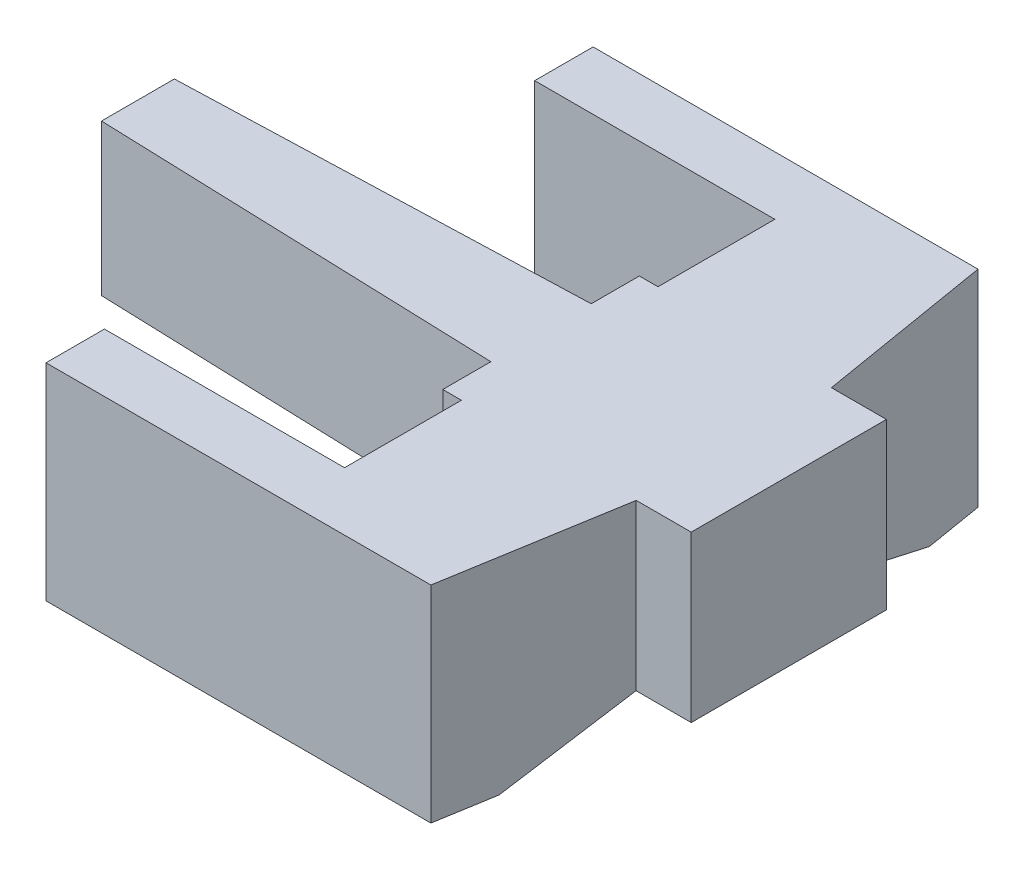
SolidWorks part; units mm, degrees
ref_plane "Front Plane" through (0, 0, 0) normal (0, 0, 1) x (1, 0, 0)
ref_plane "Top Plane" through (0, 0, 0) normal (0, 1, 0) x (1, 0, 0)
ref_plane "Right Plane" through (0, 0, 0) normal (1, 0, 0) x (0, 0, -1)
sketch "Sketch1" plane through (0, 0, 0) normal (0, 1, 0) x (1, 0, 0)
  line L0 (167.303, 457.5748) -> (832.0476, 457.5748) construction
  line L2 (53.2314, 93.5629) -> (55.3687, 80.7629)
  line L3 (55.3687, 80.7629) -> (59.3687, 80.7629)
  line L4 (59.3687, 80.7629) -> (59.3687, 66.5629)
  line L5 (59.3687, 66.5629) -> (55.3687, 66.5629)
  line L6 (55.3687, 66.5629) -> (53.2314, 53.7629)
  line L7 (53.2314, 53.7629) -> (25.2314, 53.7629)
  line L8 (25.2314, 53.7629) -> (25.2314, 58.0129)
  line L9 (25.2314, 58.0129) -> (42.7011, 58.0129)
  line L10 (42.7011, 58.0129) -> (42.7011, 66.5129)
  line L11 (42.7011, 66.5129) -> (41.345, 66.5129)
  line L12 (41.345, 66.5129) -> (41.345, 70.0129)
  line L13 (41.345, 70.0129) -> (12.0187, 71.0129)
  line L14 (12.0187, 71.0129) -> (12.0187, 76.3129)
  line L15 (12.0187, 76.3129) -> (41.345, 77.3129)
  line L16 (41.345, 77.3129) -> (41.345, 80.8129)
  line L17 (41.345, 80.8129) -> (42.7011, 80.8129)
  line L18 (42.7011, 80.8129) -> (42.7011, 89.3129)
  line L19 (42.7011, 89.3129) -> (25.2314, 89.3129)
  line L20 (25.2314, 89.3129) -> (25.2314, 93.5629)
  line L21 (25.2314, 93.5629) -> (53.2314, 93.5629)
  point P2 (0, 0)
  dimension "D1" = 47.35
  dimension "D2" = 39.8
  dimension "D3" = 4.25
  dimension "D4" = 4.25
  dimension "D5" = 12
  dimension "D6" = 12
  dimension "D7" = 3.5
  dimension "D8" = 3.5
  dimension "D9" = 1.3562
  dimension "D10" = 1.3562
  dimension "D11" = 13
  dimension "D12" = 13
  dimension "D13" = 28
  dimension "D14" = 28
  dimension "D15" = 12.8
  dimension "D16" = 12.8
  dimension "D17" = 4
  dimension "D18" = 4
extrude "Boss-Extrude1" add sketch "Sketch1" along normal blind 15
sketch "Sketch2" plane through (0, 0, 0) normal (0, -1, 0) x (1, 0, 0)
  circle A0 centre (42.7011, -73.6629) radius 2.5
extrude "Boss-Extrude2" add sketch "Sketch2" along normal blind 1
sketch "Sketch3" plane through (0, 0, 0) normal (0, -1, 0) x (-1, 0, 0)
  line L0 (-42.7011, 80.8129) -> (-55.3687, 80.7629)
  line L1 (-55.3687, 80.7629) -> (-59.3687, 80.7629)
  line L2 (-59.3687, 80.7629) -> (-59.3687, 66.5629)
  line L3 (-59.3687, 66.5629) -> (-41.345, 66.5129)
  line L4 (-41.345, 66.5129) -> (-41.345, 70.0129)
  line L5 (-41.345, 70.0129) -> (-41.345, 71.5627)
  line L6 (-42.7011, 80.8129) -> (-41.345, 80.8129)
  line L7 (-42.7011, 80.8129) -> (-41.345, 80.8129) construction
  line L8 (-41.345, 80.8129) -> (-41.345, 77.3129) construction
  line L9 (-41.345, 80.8129) -> (-41.345, 77.3129)
  line L10 (-41.345, 77.3129) -> (-41.345, 75.7631)
  circle A0 centre (-42.7011, 73.6629) radius 2.5 construction
  arc A1 (-41.345, 75.7631) -> (-41.345, 71.5627) centre (-42.7011, 73.6629) ccw
extrude "Cut-Extrude1" cut sketch "Sketch3" against normal blind 3
sketch "Sketch4" plane through (0, 0, 0) normal (0, -1, 0) x (1, 0, 0)
  line L0 (41.345, -77.3129) -> (12.0187, -76.3129)
  line L1 (12.0187, -76.3129) -> (12.0187, -71.0129)
  line L2 (12.0187, -71.0129) -> (41.345, -70.0129)
  line L3 (41.345, -70.0129) -> (41.345, -71.5627)
  line L4 (41.345, -77.2209) -> (41.345, -75.7631)
  line L5 (41.345, -75.7631) -> (41.345, -77.3129) construction
  arc A0 (41.345, -71.5627) -> (41.345, -75.7631) centre (42.7011, -73.6629) ccw
extrude "Cut-Extrude5" cut sketch "Sketch4" against normal blind 3 and the other way through all
sketch "Sketch5" plane through (0, 0, -66.5129) normal (0, 0, 1) x (1, 0, 0)
  line L1 (41.345, 3) -> (42.7011, 3)
  line L2 (41.345, 3) -> (41.345, 0)
  line L3 (41.345, 0) -> (42.7011, 0)
  line L4 (42.7011, 3) -> (42.7011, 0)
extrude "Cut-Extrude6" cut sketch "Sketch5" against normal blind 3
sketch "Sketch7" plane through (42.7011, 0, 0) normal (-1, 0, 0) x (0, 0, 1)
  line L0 (-66.5167, 0) -> (-67.2906, 0)
  line L1 (-66.5129, 3) -> (-58.0129, 0)
  line L2 (-58.0129, 0) -> (-66.5167, 0)
  line L3 (-67.2906, 0) -> (-67.2906, 3)
  line L4 (-89.3129, 0) -> (-80.8129, 0)
  line L5 (-67.2906, 3) -> (-66.5129, 3)
  line L6 (-80.8129, 3) -> (-89.3129, 0)
  line L7 (-80.8129, 3) -> (-79.7132, 3)
  line L8 (-79.7132, 3) -> (-79.7132, 0)
  line L9 (-79.7132, 0) -> (-80.8129, 0)
  line L11 (-58.0129, 15) -> (-58.0129, 0) construction
  dimension "D1" = 9.2777
  dimension "D2" = 21.7003
extrude "Cut-Extrude11" cut sketch "Sketch7" against normal blind 20
sketch "Sketch11" plane through (0, 3, 0) normal (0, -1, 0) x (1, 0, 0)
  line L0 (41.345, -77.3129) -> (41.345, -75.7631)
  line L1 (41.345, -77.3129) -> (12.0187, -76.3129)
  line L2 (12.0187, -76.3129) -> (12.0187, -71.0129)
  line L3 (12.0187, -71.0129) -> (41.345, -70.0129)
  line L4 (41.345, -70.0129) -> (41.345, -71.5627)
  arc A0 (41.345, -71.5627) -> (41.345, -75.7631) centre (42.7011, -73.6629) ccw
extrude "Cut-Extrude12" cut sketch "Sketch11" against normal blind 1
